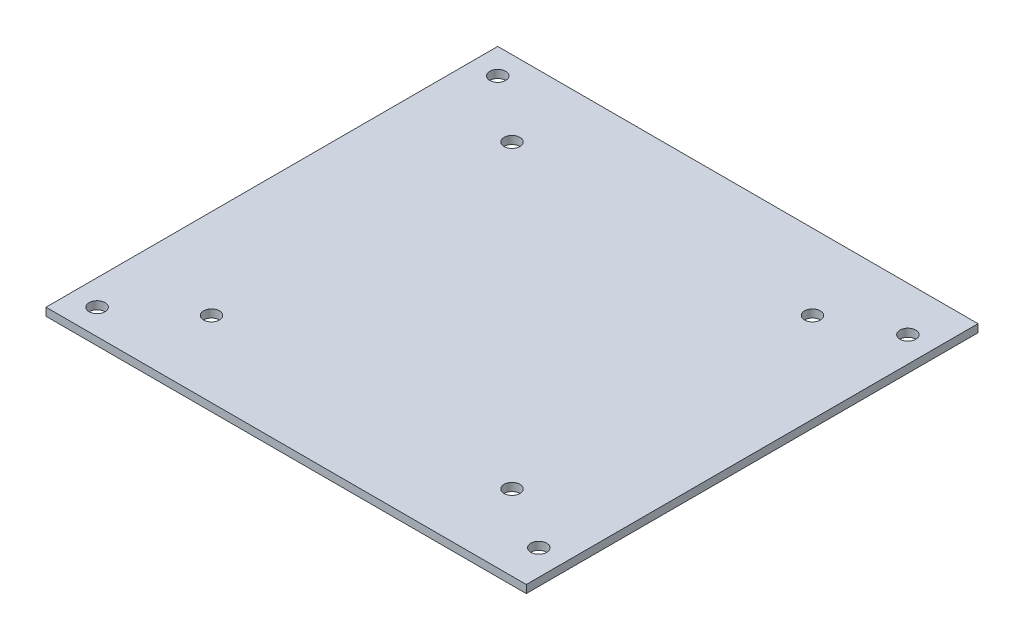
SolidWorks part; units mm, degrees
material "5052-H38"
ref_plane "Front Plane" through (0, 0, 0) normal (0, 0, 1) x (1, 0, 0)
ref_plane "Top Plane" through (0, 0, 0) normal (0, 1, 0) x (1, 0, 0)
ref_plane "Right Plane" through (0, 0, 0) normal (1, 0, 0) x (0, 0, -1)
sketch "Sketch2" plane through (0, 0, 0) normal (0, 1, 0) x (1, 0, 0)
  line L1 (-47.95, -45.1) -> (47.95, -45.1)
  line L2 (-47.95, -45.1) -> (-47.95, 45.1)
  line L3 (-47.95, 45.1) -> (47.95, 45.1)
  line L4 (47.95, -45.1) -> (47.95, 45.1)
  line L5 (-47.95, -45.1) -> (47.95, 45.1) construction
  line L6 (-47.95, 45.1) -> (47.95, -45.1) construction
  circle A0 centre (30, 30) radius 1.5875
  circle A1 centre (30, -30) radius 1.5875
  circle A2 centre (-30, -30) radius 1.5875
  circle A3 centre (-30, 30) radius 1.5875
  circle A4 centre (-42.85, 40) radius 1.5875
  circle A5 centre (-42.85, -40) radius 1.5875
  circle A6 centre (42.85, 36.2) radius 1.5875
  circle A7 centre (42.85, -37.5) radius 1.5875
  point P0 (0, 0)
  point P6 (30, 30)
  point P9 (42.85, 36.2)
  point P10 (42.85, -37.5)
  point P11 (-42.85, 40)
  point P18 (0, 0)
  point P19 (-42.85, -40)
  dimension "D1" = 4
extrude "Boss-Extrude1" add sketch "Sketch2" along normal blind 1.58 contours A2 | A5 | A3 | A6 | A0 | A1 | A7 | A4 | L2 L1 L4 L3
